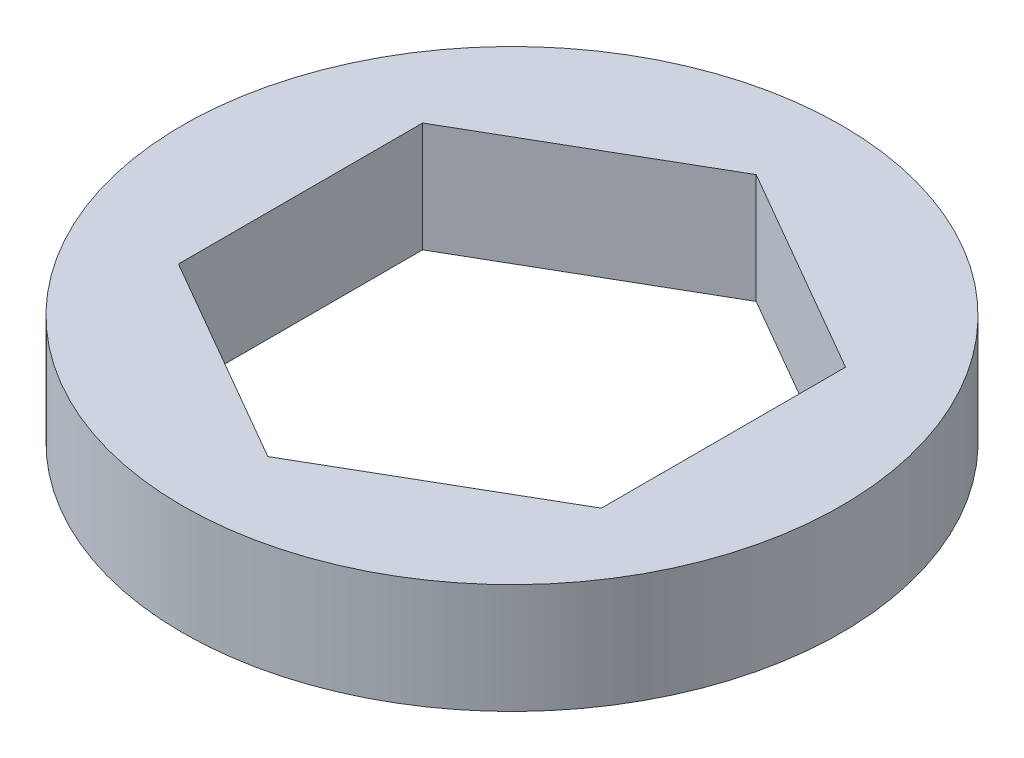
SolidWorks part; units mm, degrees
material "Markforged"
ref_plane "Front Plane" through (0, 0, 0) normal (0, 0, 1) x (1, 0, 0)
ref_plane "Top Plane" through (0, 0, 0) normal (0, 1, 0) x (1, 0, 0)
ref_plane "Right Plane" through (0, 0, 0) normal (1, 0, 0) x (0, 0, -1)
other "Bounding Box"
ref_plane "Default Plane" through (-8.9266, -12.7485, 0) normal (-0.1736, 0.9848, 0) x (0.9848, 0.1736, 0)
sketch "Sketch1" plane through (0, 0, 0) normal (0, 1, 0) x (1, 0, 0)
  line L1 (4.8895, -2.823) -> (4.8895, 2.823)
  line L2 (4.8895, 2.823) -> (0, 5.6459)
  line L3 (0, 5.6459) -> (-4.8895, 2.823)
  line L4 (-4.8895, 2.823) -> (-4.8895, -2.823)
  line L5 (-4.8895, -2.823) -> (0, -5.6459)
  line L6 (0, -5.6459) -> (4.8895, -2.823)
  circle A0 centre (0, 0) radius 4.8895 construction
  circle A1 centre (0, 0) radius 7.62
  dimension "D1" = 15.24
  dimension "D2" = 9.779
extrude "Boss-Extrude1" add sketch "Sketch1" along normal mid plane 2.54
